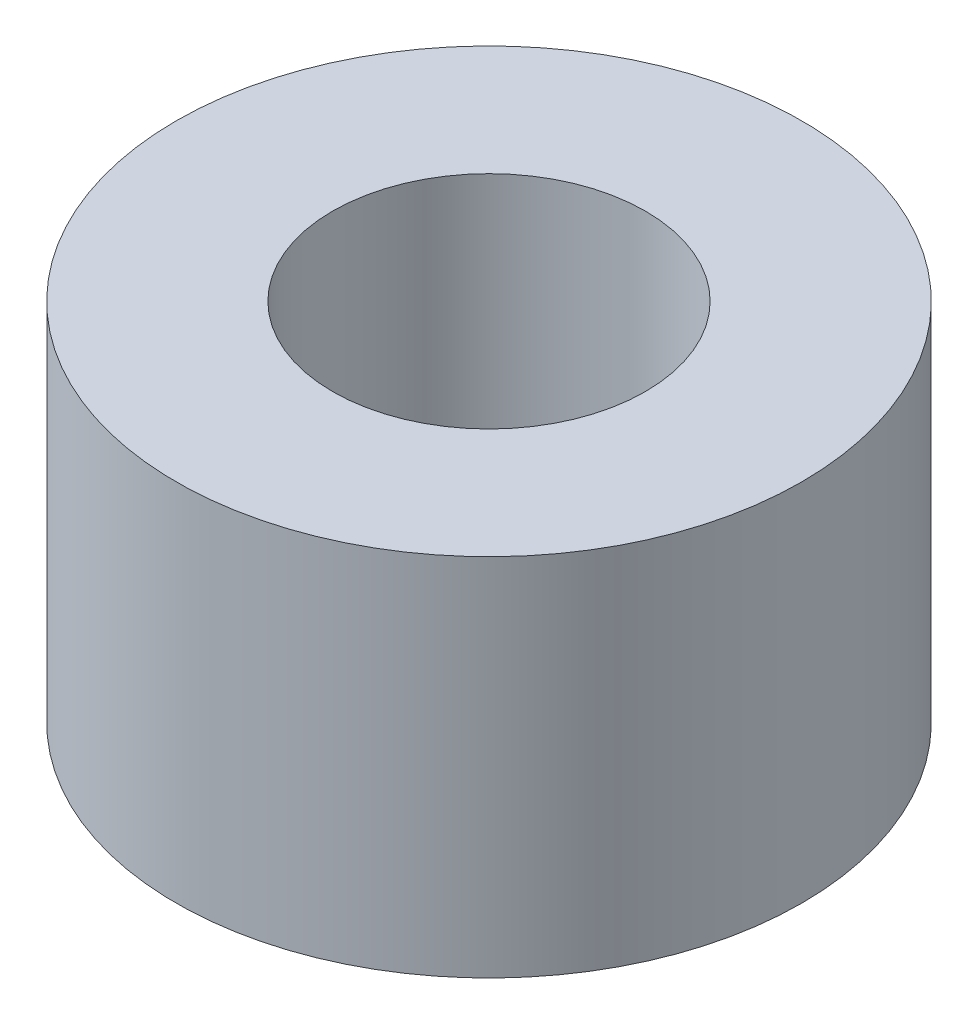
SolidWorks part; units mm, degrees
ref_plane "Front Plane" through (0, 0, 0) normal (0, 0, 1) x (1, 0, 0)
ref_plane "Top Plane" through (0, 0, 0) normal (0, 1, 0) x (1, 0, 0)
ref_plane "Right Plane" through (0, 0, 0) normal (1, 0, 0) x (0, 0, -1)
sketch "Sketch1" plane through (0, 0, 0) normal (0, 1, 0) x (1, 0, 0)
  circle A0 centre (0, 0) radius 30
  dimension "D1" = 60
extrude "Extrude-Thin1" add sketch "Sketch1" along normal blind 70 thin
